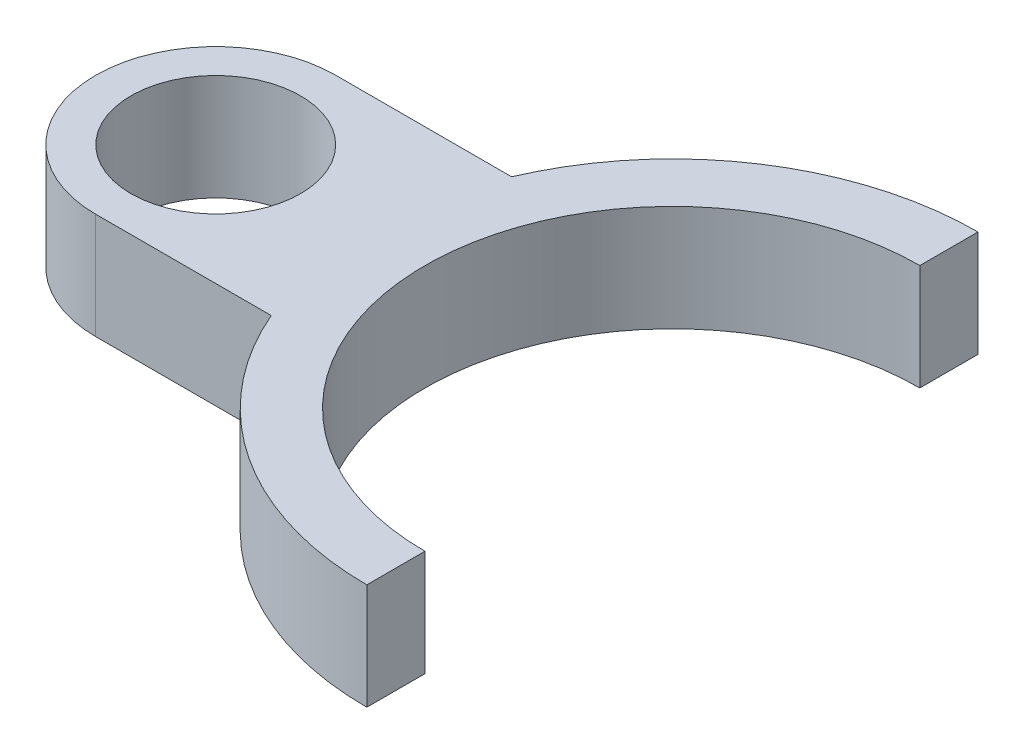
SolidWorks part; units mm, degrees
ref_plane "Front Plane" through (0, 0, 0) normal (0, 0, 1) x (1, 0, 0)
ref_plane "Top Plane" through (0, 0, 0) normal (0, 1, 0) x (1, 0, 0)
ref_plane "Right Plane" through (0, 0, 0) normal (1, 0, 0) x (0, 0, -1)
sketch "Sketch1" plane through (0, 0, 0) normal (0, 1, 0) x (1, 0, 0)
  circle A0 centre (0, 0) radius 12
  circle A1 centre (0, 0) radius 17.0007
extrude "Boss-Extrude1" add sketch "Sketch1" along normal blind 15
sketch "Sketch2" plane through (0, 15, 0) normal (0, 1, 0) x (1, 0, 0)
  line L0 (0, 17.0007) -> (25, 17.0007)
  line L1 (25, 17.0007) -> (25, -17.0007)
  line L2 (25, -17.0007) -> (0, -17.0007)
  circle A0 centre (0, 0) radius 17.0007 construction
  arc A1 (0, -17.0007) -> (0, 17.0007) centre (0, 0) ccw
  dimension "D1" = 25
extrude "Boss-Extrude2" add sketch "Sketch2" against normal blind 15
sketch "Sketch3" plane through (0, 0, 0) normal (0, -1, 0) x (-1, 0, 0)
  line L0 (-64.598, -35) -> (-64.598, -43.2282)
  line L1 (-64.598, -43.2282) -> (-64.598, 43.2282)
  circle A0 centre (-64.598, 0) radius 43.2282
  circle A1 centre (-64.598, 0) radius 35
extrude "Boss-Extrude3" add sketch "Sketch3" against normal blind 15
